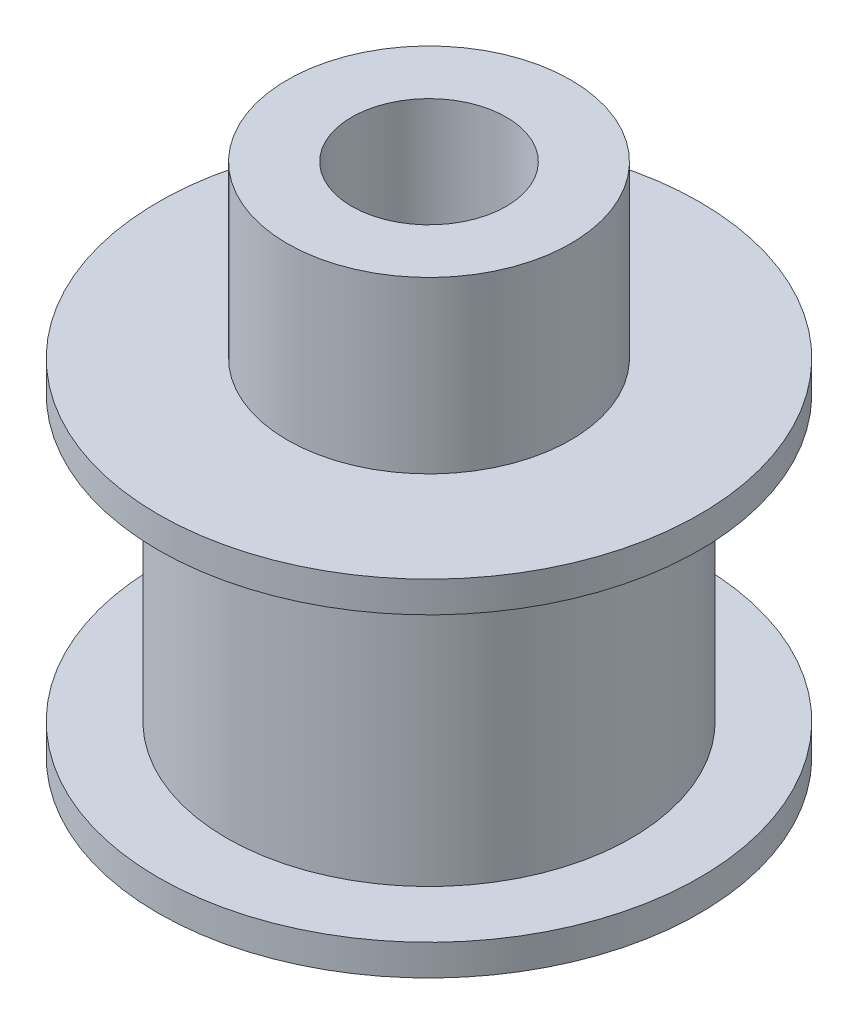
SolidWorks part; units mm, degrees
ref_plane "Front Plane" through (0, 0, 0) normal (0, 0, 1) x (1, 0, 0)
ref_plane "Top Plane" through (0, 0, 0) normal (0, 1, 0) x (1, 0, 0)
ref_plane "Right Plane" through (0, 0, 0) normal (1, 0, 0) x (0, 0, -1)
sketch "Sketch1" plane through (0, 0, 0) normal (0, 1, 0) x (1, 0, 0)
  circle A0 centre (0, 0) radius 10.5
  dimension "D1" = 21
extrude "Boss-Extrude1" add sketch "Sketch1" along normal blind 1.2
sketch "Sketch2" plane through (0, 1.2, 0) normal (0, 1, 0) x (1, 0, 0)
  circle A0 centre (0, 0) radius 7.85
  dimension "D1" = 15.7
extrude "Boss-Extrude2" add sketch "Sketch2" along normal blind 11
sketch "Sketch3" plane through (0, 12.2, 0) normal (0, 1, 0) x (1, 0, 0)
  circle A0 centre (0, 0) radius 10.5
  dimension "D1" = 21
extrude "Boss-Extrude3" add sketch "Sketch3" along normal blind 1.2
sketch "Sketch4" plane through (0, 13.4, 0) normal (0, 1, 0) x (1, 0, 0)
  circle A0 centre (0, 0) radius 5.5
  dimension "D1" = 11
extrude "Boss-Extrude4" add sketch "Sketch4" along normal blind 6.6
sketch "Sketch5" plane through (0, 20, 0) normal (0, 1, 0) x (1, 0, 0)
  circle A0 centre (0, 0) radius 3
  dimension "D1" = 6
extrude "Cut-Extrude1" cut sketch "Sketch5" against normal through all
